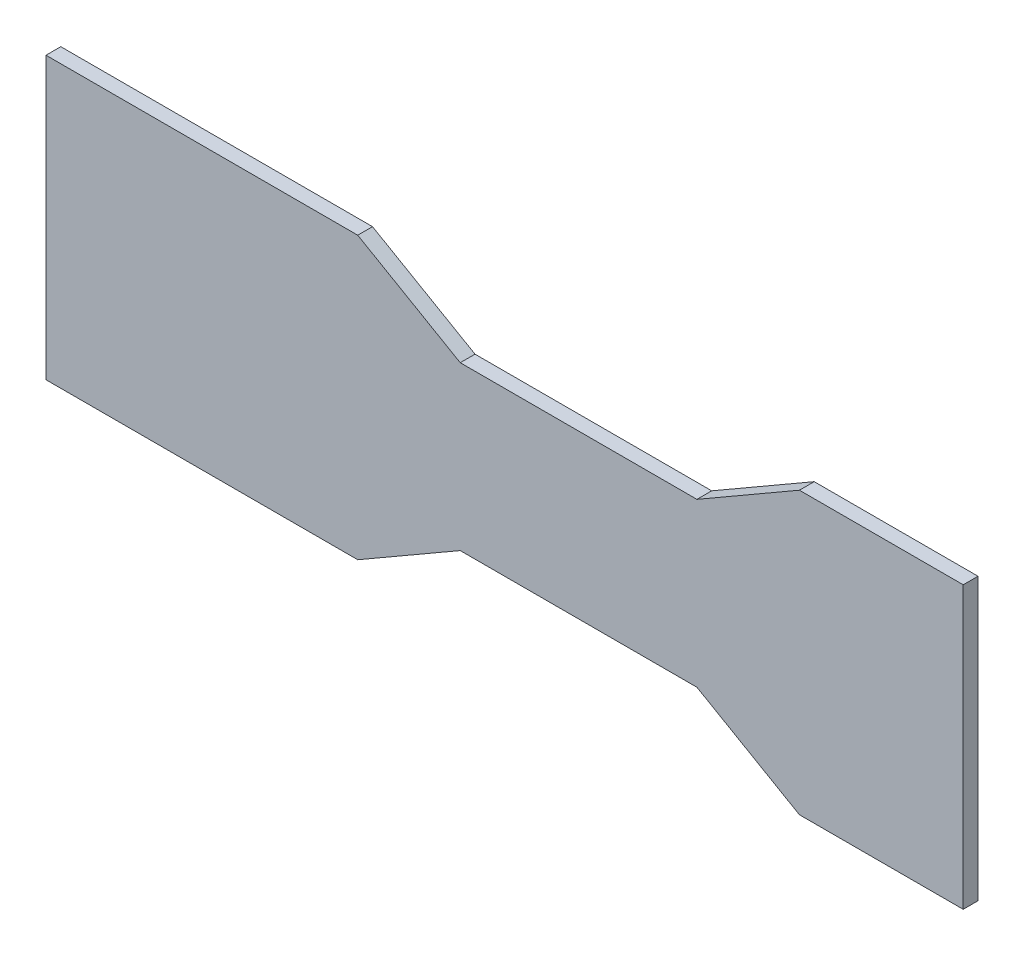
SolidWorks part; units mm, degrees
ref_plane "Front Plane" through (0, 0, 0) normal (0, 0, 1) x (1, 0, 0)
ref_plane "Top Plane" through (0, 0, 0) normal (0, 1, 0) x (1, 0, 0)
ref_plane "Right Plane" through (0, 0, 0) normal (1, 0, 0) x (0, 0, -1)
sketch "Sketch1" plane through (0, 0, 0) normal (0, 0, 1) x (1, 0, 0)
  line L1 (0, 0) -> (393.7, 0)
  line L2 (0, 0) -> (0, 120.65)
  line L3 (0, 120.65) -> (393.7, 120.65)
  line L4 (393.7, 0) -> (393.7, 120.65)
  dimension "D1" = 120.65
  dimension "D2" = 393.7
extrude "Boss-Extrude1" add sketch "Sketch1" along normal blind 6.35
sketch "Sketch2" plane through (0, 0, 6.35) normal (0, 0, 1) x (1, 0, 0)
  line L0 (133.8059, 120.65) -> (177.8, 95.25)
  line L1 (393.7, 120.65) -> (0, 120.65) construction
  line L2 (177.8, 95.25) -> (279.4, 95.25)
  line L3 (279.4, 95.25) -> (323.3941, 120.65)
  line L4 (323.3941, 120.65) -> (133.8059, 120.65)
  line L5 (133.8059, 0) -> (177.8, 25.4)
  line L6 (0, 0) -> (393.7, 0) construction
  line L7 (177.8, 25.4) -> (279.4, 25.4)
  line L8 (279.4, 25.4) -> (323.3941, 0)
  line L9 (323.3941, 0) -> (133.8059, 0)
  line L10 (325.0956, 114.3) -> (321.9206, 119.7993) construction
  line L11 (393.7, 120.65) -> (325.0956, 120.65) construction
  line L12 (393.7, 120.65) -> (393.7, 114.3) construction
  line L13 (393.7, 114.3) -> (325.0956, 114.3) construction
  line L14 (325.0956, 120.65) -> (325.0956, 114.3) construction
  line L15 (132.1044, 114.3) -> (135.2794, 119.7993) construction
  line L16 (0, 120.65) -> (132.1044, 120.65) construction
  line L17 (0, 120.65) -> (0, 114.3) construction
  line L18 (0, 114.3) -> (132.1044, 114.3) construction
  line L19 (132.1044, 120.65) -> (132.1044, 114.3) construction
  line L20 (393.7, 0) -> (393.7, 120.65) construction
  line L21 (177.8, 25.4) -> (177.8, 95.25) construction
  dimension "D3" = 25.4
  dimension "D4" = 25.4
  dimension "D5" = 114.3
  dimension "D6" = 6.35
  dimension "D7" = 150
  dimension "D8" = 101.6
  dimension "D9" = 150
extrude "Cut-Extrude1" cut sketch "Sketch2" against normal through all
